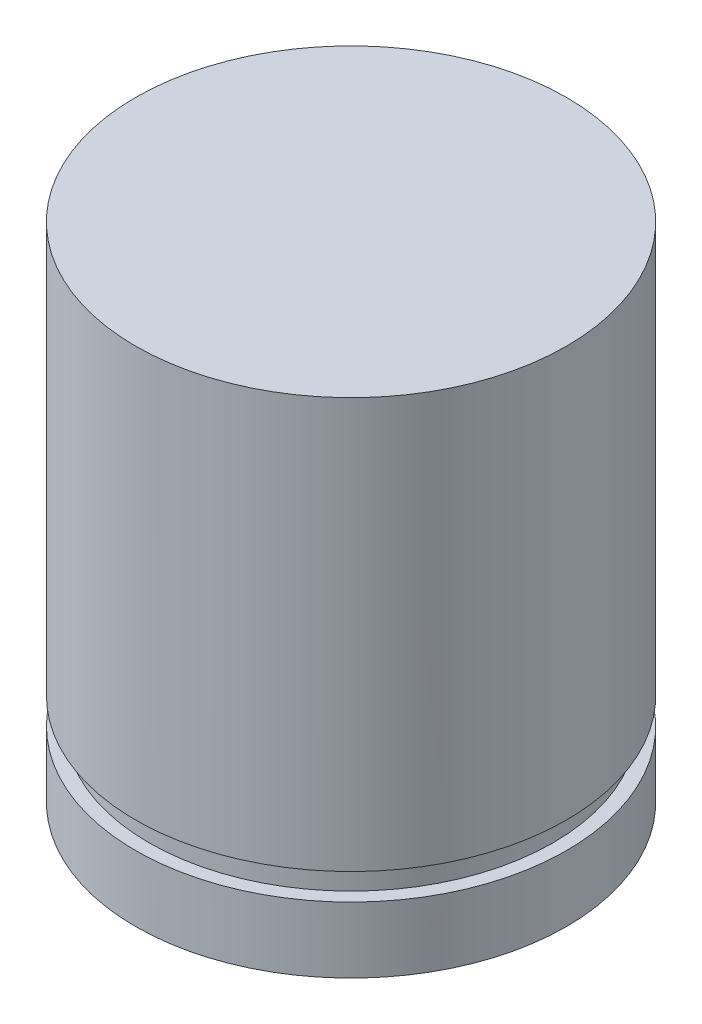
SolidWorks part; units mm, degrees
material "AISI 1020"
ref_plane "Front Plane" through (0, 0, 0) normal (0, 0, 1) x (1, 0, 0)
ref_plane "Top Plane" through (0, 0, 0) normal (0, 1, 0) x (1, 0, 0)
ref_plane "Right Plane" through (0, 0, 0) normal (1, 0, 0) x (0, 0, -1)
sketch "Sketch1" plane through (0, 0, 0) normal (0, 1, 0) x (1, 0, 0)
  circle A0 centre (0, 0) radius 6
extrude "Boss-Extrude1" add sketch "Sketch1" along normal blind 14
ref_plane "Plane1" through (0, 2.57, 0) normal (0, 1, 0) x (1, 0, 0)
sketch "Sketch2" plane through (0, 2.57, 0) normal (0, 1, 0) x (1, 0, 0)
  line L0 (-7.9155, 6.7723) -> (-7.7486, -7.9989)
  line L1 (-7.7486, -7.9989) -> (10.3957, -7.9989)
  line L2 (10.3957, -7.9989) -> (9.1533, 7.8408)
  line L3 (9.1533, 7.8408) -> (-7.9155, 6.7723)
  circle A0 centre (0, 0) radius 5.6261
  dimension "D1" = 11.2522
extrude "Cut-Extrude1" cut sketch "Sketch2" against normal blind 0.7366
